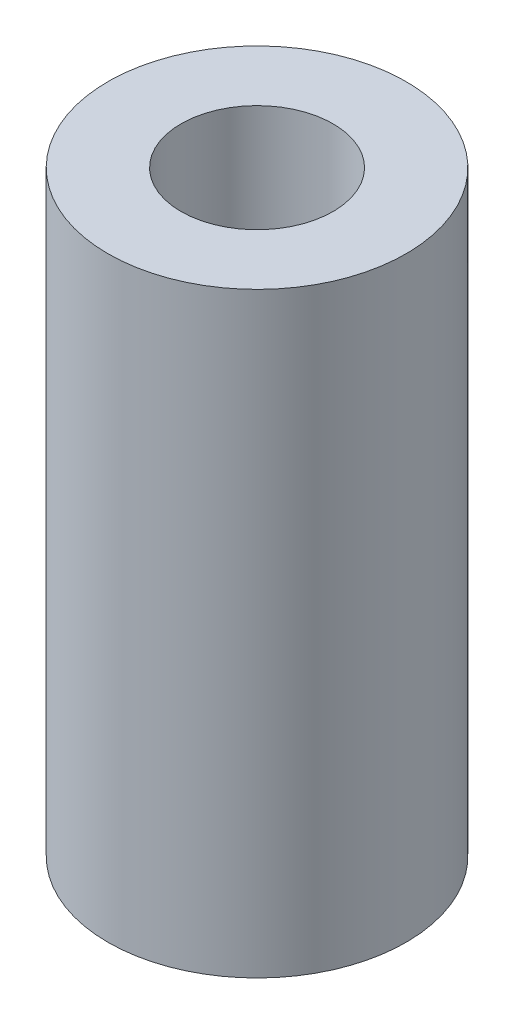
SolidWorks part; units mm, degrees
ref_plane "Front Plane" through (0, 0, 0) normal (0, 0, 1) x (1, 0, 0)
ref_plane "Top Plane" through (0, 0, 0) normal (0, 1, 0) x (1, 0, 0)
ref_plane "Right Plane" through (0, 0, 0) normal (1, 0, 0) x (0, 0, -1)
sketch "Sketch1" plane through (0, 0, 0) normal (0, 1, 0) x (1, 0, 0)
  circle A0 centre (0, 0) radius 6.35
  dimension "D1" = 12.7
extrude "Boss-Extrude1" add sketch "Sketch1" along normal blind 25.4
sketch "Sketch2" plane through (0, 0, 0) normal (0, -1, 0) x (1, 0, 0)
  circle A0 centre (0, 0) radius 3.048
  dimension "D1" = 6.096
extrude "Cut-Extrude1" cut sketch "Sketch2" against normal blind 8.636
sketch "Sketch3" plane through (0, 25.4, 0) normal (0, 1, 0) x (1, 0, 0)
  circle A0 centre (0, 0) radius 3.2385
  dimension "D1" = 6.477
extrude "Cut-Extrude2" cut sketch "Sketch3" against normal blind 12.7
